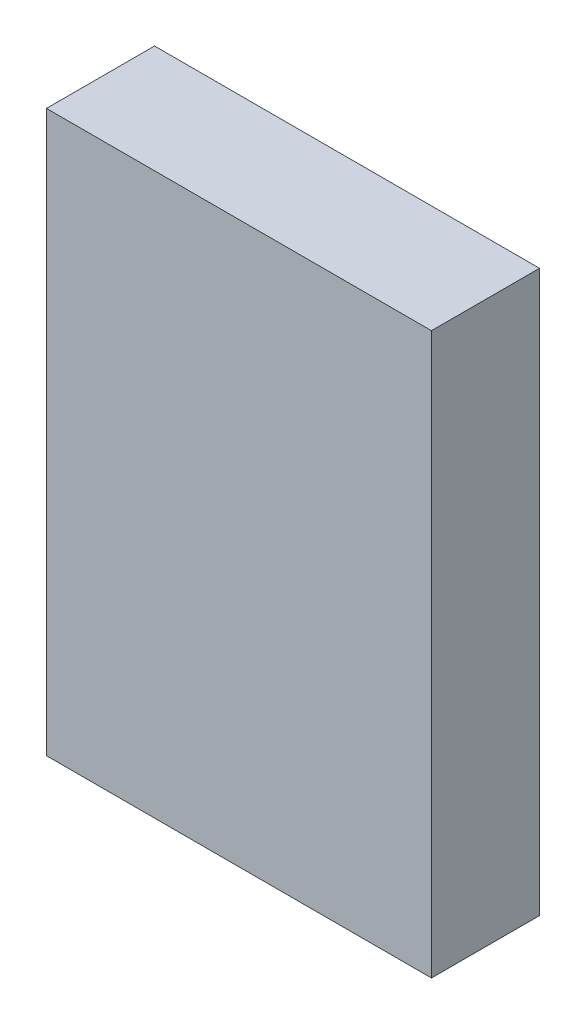
SolidWorks part; units mm, degrees
ref_plane "Front Plane" through (0, 0, 0) normal (1, 0, 0) x (0, 1, 0)
ref_plane "Top Plane" through (0, 0, 0) normal (0, 0, 1) x (0, 1, 0)
ref_plane "Right Plane" through (0, 0, 0) normal (0, 1, 0) x (-1, 0, 0)
sketch "Sketch1" plane through (0, 0, 0) normal (0, 0, 1) x (0, 1, 0)
  line L1 (0, 0) -> (83, 0)
  line L2 (0, 0) -> (0, 57)
  line L3 (0, 57) -> (83, 57)
  line L4 (83, 0) -> (83, 57)
  dimension "D1" = 83
  dimension "D2" = 57
extrude "Boss-Extrude1" add sketch "Sketch1" along normal blind 16
